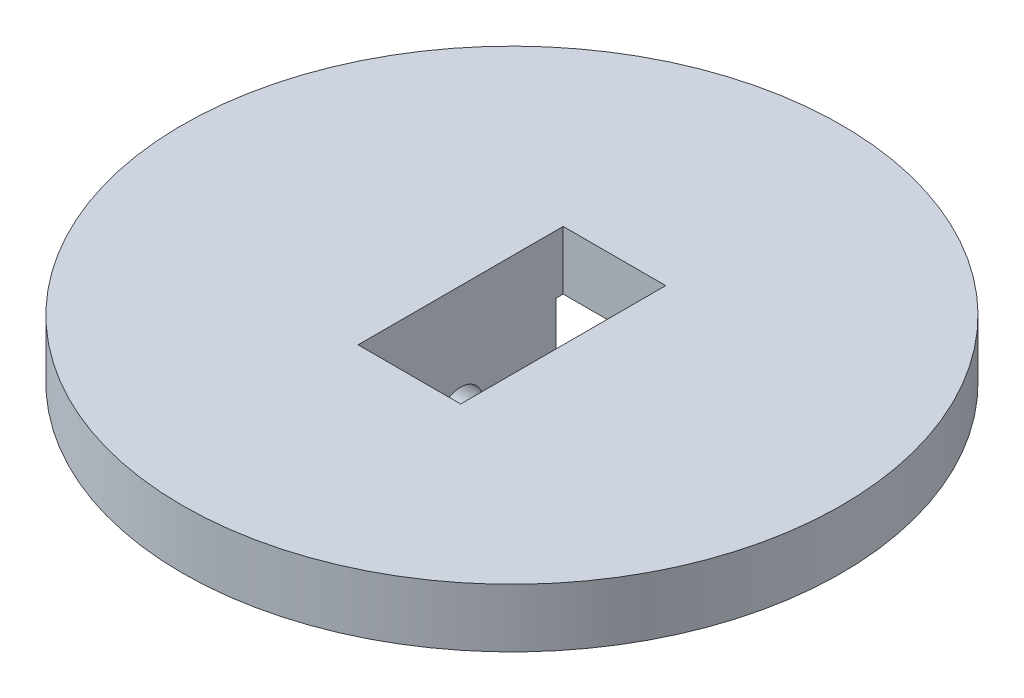
SolidWorks part; units mm, degrees
ref_plane "Front Plane" through (0, 0, 0) normal (0, 0, 1) x (1, 0, 0)
ref_plane "Top Plane" through (0, 0, 0) normal (0, 1, 0) x (1, 0, 0)
ref_plane "Right Plane" through (0, 0, 0) normal (1, 0, 0) x (0, 0, -1)
sketch "Sketch1" plane through (0, 0, 0) normal (0, 1, 0) x (1, 0, 0)
  circle A0 centre (0, 0) radius 22.5
  point P8 (0, 0)
  dimension "D1" = 45
extrude "Boss-Extrude1" add sketch "Sketch1" along normal blind 4
sketch "Sketch3" plane through (0, 0, 0) normal (0, 0, 1) x (1, 0, 0)
  line L1 (-7, 4) -> (7, 4)
  line L2 (-7, 4) -> (-7, -7)
  line L3 (-7, -7) -> (7, -7)
  line L4 (7, 4) -> (7, -7)
  point P6 (0, 4)
  dimension "D1" = 14
  dimension "D2" = 11
extrude "Boss-Extrude2" add sketch "Sketch3" along normal mid plane 13
sketch "Sketch4" plane through (0, 0, 0) normal (0, 1, 0) x (1, 0, 0)
  line L1 (-3.5, 7) -> (3.5, 7)
  line L2 (-3.5, 7) -> (-3.5, -7)
  line L3 (-3.5, -7) -> (3.5, -7)
  line L4 (3.5, 7) -> (3.5, -7)
  point P4 (0, 7)
  point P6 (3.5, 0)
  dimension "D1" = 14
  dimension "D2" = 7
extrude "Cut-Extrude1" cut sketch "Sketch4" against normal through all both and the other way through all
sketch "Sketch5" plane through (0, 0, 0) normal (1, 0, 0) x (0, 0, -1)
  line L0 (-6.5, -7) -> (-6.5, 0) construction
  circle A0 centre (0, -3.5) radius 1.5
  point P2 (0, 0)
  point P5 (-6.5, -3.5)
  dimension "D1" = 3
extrude "Cut-Extrude2" cut sketch "Sketch5" against normal through all both and the other way through all
